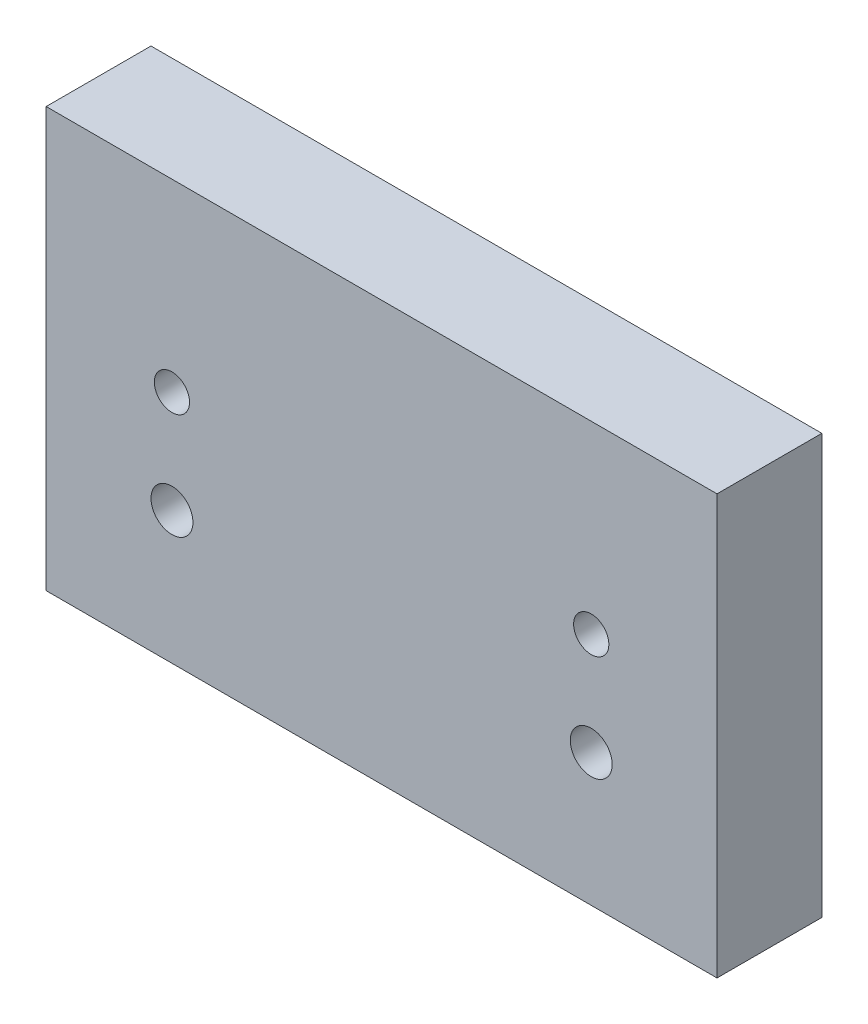
SolidWorks part; units mm, degrees
material "1023 Листовая углеродистая сталь (SS)"
ref_plane "Front" through (0, 0, 0) normal (0, 0, 1) x (1, 0, 0)
ref_plane "Top" through (0, 0, 0) normal (0, 1, 0) x (1, 0, 0)
ref_plane "Right" through (0, 0, 0) normal (1, 0, 0) x (0, 0, -1)
sketch "Sketch1" plane through (0, 0, 0) normal (0, 0, 1) x (1, 0, 0)
  line L1 (-40, 25) -> (40, 25)
  line L2 (-40, 25) -> (-40, -25)
  line L3 (-40, -25) -> (40, -25)
  line L4 (40, 25) -> (40, -25)
  line L5 (-40, 25) -> (40, -25) construction
  line L6 (-40, -25) -> (40, 25) construction
  point P0 (0, 0)
  dimension "D1" = 50
  dimension "D2" = 80
extrude "Extrude1" add sketch "Sketch1" along normal blind 12.5
hole_wizard "M6 Tapped Hole1" positions "Sketch3" profile "Sketch4" tap size "M6" standard "DIN" end condition through all
sketch "Sketch3" plane through (0, 0, 12.5) normal (0, 0, 1) x (1, 0, 0)
  point P0 (-25, -9.2063)
  point P3 (25, -9.2063)
sketch "Sketch4" plane through (-25, -9.2063, 12.5) normal (1, 0, 0) x (0, -1, 0)
  line L0 (0, 0) -> (0, 12.5)
  line L1 (0, 12.5) -> (2.5, 12.5)
  line L2 (2.5, 12.5) -> (2.5, 0)
  line L5 (2.5, 0) -> (0, 0)
  line L11 (0, -6.35) -> (0, 107.95) construction
  dimension "Диаметр проходного сверла" = 5
  dimension "Глубина проходного сверла" = 12.5
cosmetic thread "Cosmetic Thread1"
cosmetic thread "Cosmetic Thread2"
hole_wizard "M5 Tapped Hole1" positions "Sketch7" profile "Sketch8" tap size "M5" standard "DIN" end condition up to next
sketch "Sketch7" plane through (0, 0, 12.5) normal (0, 0, 1) x (1, 0, 0)
  point P0 (-25, 3)
  point P3 (25, 3)
sketch "Sketch8" plane through (-25, 3, 12.5) normal (1, 0, 0) x (0, -1, 0)
  line L0 (0, 0) -> (0, 12.5)
  line L1 (0, 12.5) -> (2.1, 12.5)
  line L2 (2.1, 12.5) -> (2.1, 0)
  line L5 (2.1, 0) -> (0, 0)
  line L11 (0, -6.35) -> (0, 107.95) construction
  dimension "Диаметр проходного сверла" = 4.2
  dimension "Глубина проходного сверла" = 12.5
cosmetic thread "Cosmetic Thread3"
cosmetic thread "Cosmetic Thread4"
